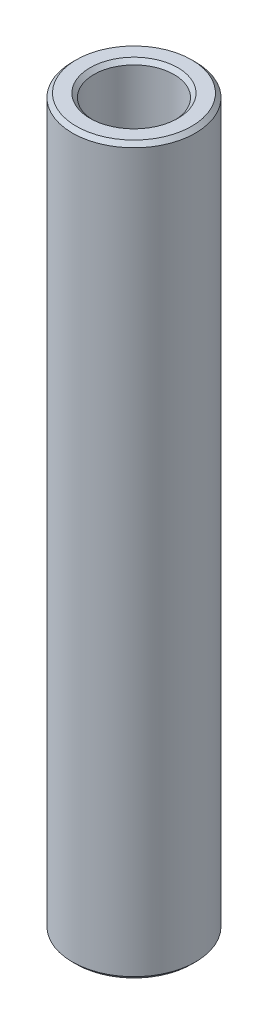
SolidWorks part; units mm, degrees
ref_plane "Front Plane" through (0, 0, 0) normal (0, 0, 1) x (1, 0, 0)
ref_plane "Top Plane" through (0, 0, 0) normal (0, 1, 0) x (1, 0, 0)
ref_plane "Right Plane" through (0, 0, 0) normal (1, 0, 0) x (0, 0, -1)
sketch "Sketch1" plane through (0, 0, 0) normal (0, 0, 1) x (1, 0, 0)
  line L0 (0, 9.6156) -> (0, -9.6156) construction
  line L1 (1.3, -11.7869) -> (2, -11.7869)
  line L2 (2, -11.7869) -> (2, 11.7869)
  line L3 (2, 11.7869) -> (1.3, 11.7869)
  line L4 (1.3, 11.7869) -> (1.3, -11.7869)
  point P7 (1.3, 0)
  dimension "D1" = 23.5737
  dimension "D2" = 4
  dimension "D3" = 2.6
revolve "Revolve1" add sketch "Sketch1" angle 360 about L0
chamfer "Chamfer1" distance 0.127 angle 45 4 edges at (0, -11.7869, 1.3) (0, -11.7869, 2) (0, 11.7869, 2) (0, 11.7869, 1.3)
